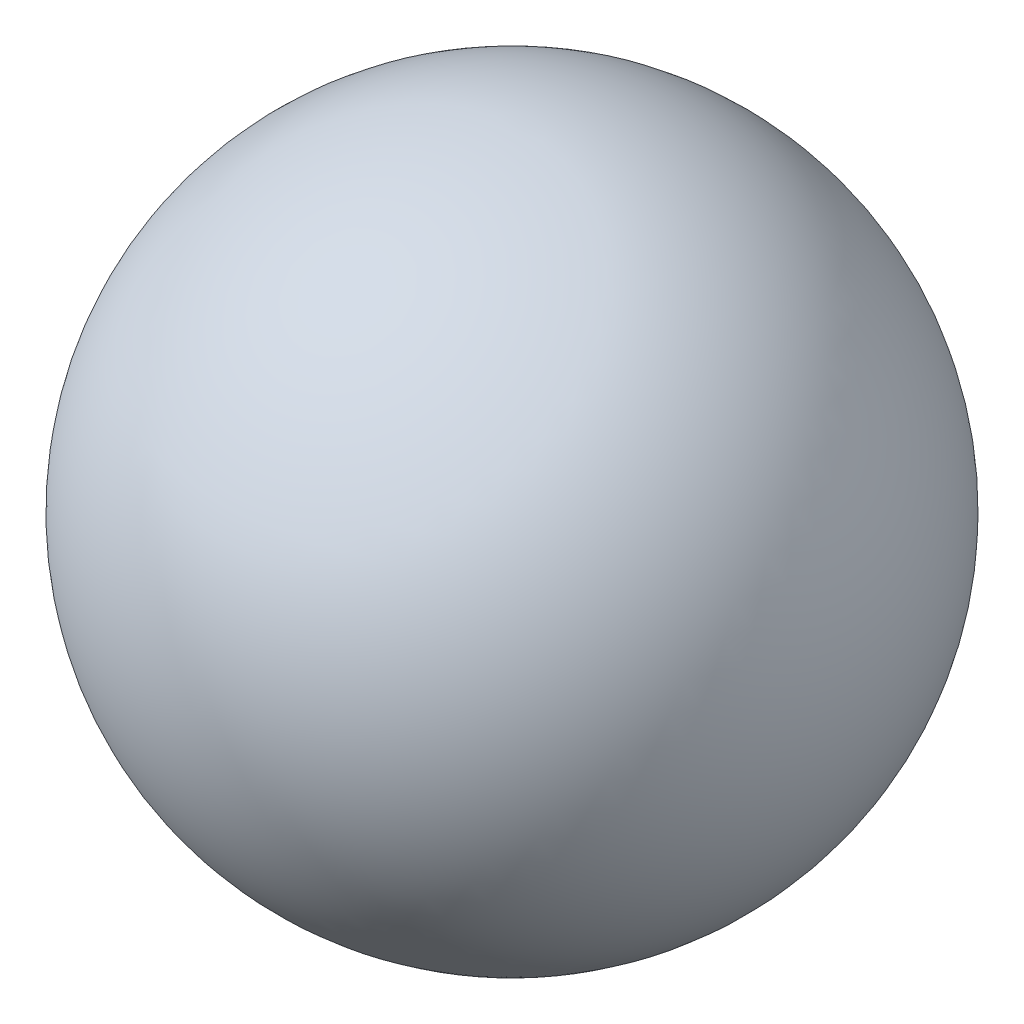
SolidWorks part; units mm, degrees
ref_plane "Front Plane" through (0, 0, 0) normal (0, 0, 1) x (1, 0, 0)
ref_plane "Top Plane" through (0, 0, 0) normal (0, 1, 0) x (1, 0, 0)
ref_plane "Right Plane" through (0, 0, 0) normal (1, 0, 0) x (0, 0, -1)
sketch "Sketch1" plane through (0, 0, 0) normal (0, 0, 1) x (1, 0, 0)
  line L0 (0, -5) -> (0, 5)
  arc A0 (0, -5) -> (0, 5) centre (0, 0) ccw
  point P6 (0, 0)
  dimension "D1" = 10
revolve "Revolve3" add sketch "Sketch1" angle 360 about L0
ref_plane "Plane1" through (0, -5, 0) normal (0, -1, 0) x (-1, 0, 0)
hole_wizard "M4 Clearance Hole1" positions "Sketch2" profile "Sketch4" hole size "M4" standard "ANSI Metric"
sketch "Sketch2" plane through (0, -5, 0) normal (0, -1, 0) x (-1, 0, 0)
  point P0 (0, 0)
sketch "Sketch4" plane through (0, -5, 0) normal (1, 0, 0) x (0, 0, -1)
  line L0 (0, 0) -> (0, 8.8519)
  line L1 (0, 8.8519) -> (2.25, 7.5)
  line L2 (2.25, 7.5) -> (2.25, 0)
  line L5 (2.25, 0) -> (0, 0)
  line L10 (0, 8.8519) -> (-2.25, 7.5) construction
  line L11 (0, -6.35) -> (0, 107.95) construction
  dimension "Hole Dia." = 4.5
  dimension "Hole Depth" = 7.5
  dimension "Drill Angle" = 118
